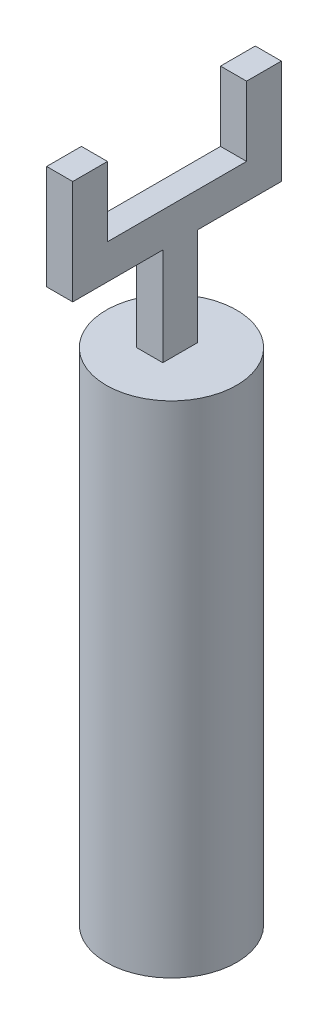
SolidWorks part; units mm, degrees
ref_plane "前视基准面" through (0, 0, 0) normal (0, 0, 1) x (1, 0, 0)
ref_plane "上视基准面" through (0, 0, 0) normal (0, 1, 0) x (1, 0, 0)
ref_plane "右视基准面" through (0, 0, 0) normal (1, 0, 0) x (0, 0, -1)
other "Configuration Table"
sketch "草图1" plane through (0, 0, 0) normal (0, 1, 0) x (1, 0, 0)
  circle A0 centre (0, 0) radius 0.75
extrude "凸台-拉伸1" add sketch "草图1" along normal blind 5.75
sketch "草图2" plane through (0, 0, 0) normal (1, 0, 0) x (0, 0, -1)
  line L0 (-1.236, 6.8734) -> (1.164, 6.8734)
  line L2 (0.2, 5.6919) -> (0.2, 6.8734)
  line L3 (-0.2, 5.6919) -> (0.2, 5.6919)
  line L5 (-0.2, 5.6919) -> (-0.2, 6.8734)
  line L6 (-1.236, 8.0734) -> (-0.836, 8.0734)
  line L7 (0.764, 8.0734) -> (1.164, 8.0734)
  line L9 (-1.236, 6.8734) -> (-1.236, 8.0734)
  line L11 (1.164, 6.8734) -> (1.164, 8.0734)
  line L12 (-0.836, 7.2734) -> (-0.836, 8.0734)
  line L13 (0.764, 7.2734) -> (-0.836, 7.2734)
  line L14 (0.764, 7.2734) -> (0.764, 8.0734)
  point P0 (0, 0)
extrude "凸台-拉伸3" add sketch "草图2" along normal blind 0.1 and the other way blind 0.2 separate body contours L5 L3 L2 L0
